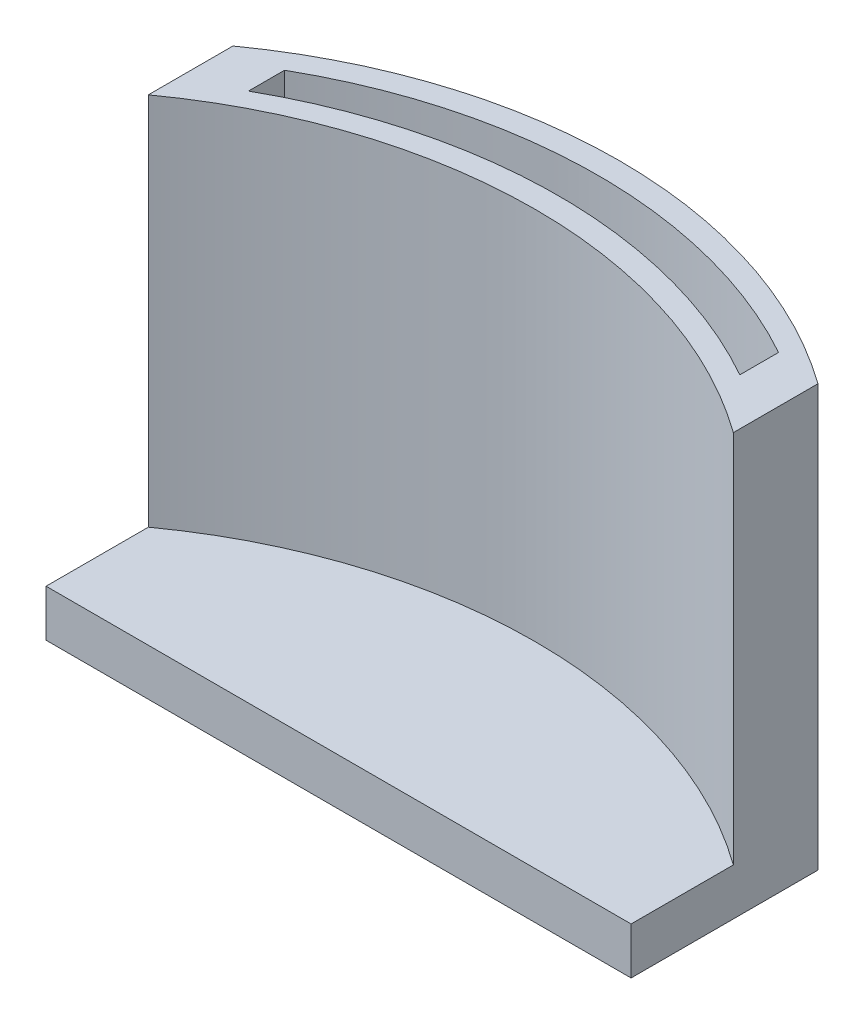
SolidWorks part; units mm, degrees
ref_plane "Front Plane" through (0, 0, 0) normal (0, 0, 1) x (1, 0, 0)
ref_plane "Top Plane" through (0, 0, 0) normal (0, 1, 0) x (1, 0, 0)
ref_plane "Right Plane" through (0, 0, 0) normal (1, 0, 0) x (0, 0, -1)
sketch "Sketch1" plane through (0, 0, 0) normal (0, 1, 0) x (1, 0, 0)
  line L1 (0, 0) -> (31.75, 0)
  line L2 (0, 0) -> (0, 26.6496)
  line L4 (31.75, 0) -> (31.75, 26.6496)
  arc A0 (0, 26.6496) -> (31.75, 26.6496) centre (15.875, 4.4945) cw
  dimension "D3" = 27.2555
  dimension "D4" = 4.4945
  dimension "D5" = 15.875
  dimension "D1" = 31.75
extrude "Boss-Extrude1" add sketch "Sketch1" along normal blind 2.54
sketch "Sketch2" plane through (0, 2.54, 0) normal (0, 1, 0) x (1, 0, 0)
  line L1 (0, 26.6496) -> (0, 0) construction
  line L3 (31.75, 0) -> (31.75, 26.6496) construction
  line L4 (31.75, 22.0596) -> (31.75, 26.6496)
  line L5 (0, 0) -> (31.75, 0) construction
  line L6 (0, 22.0596) -> (0, 26.6496)
  line L10 (2.54, 26.9117) -> (2.54, 24.9517)
  line L11 (29.21, 27.0547) -> (29.21, 24.9517)
  arc A1 (0, 22.0596) -> (31.75, 22.0596) centre (15.875, 0) cw
  arc A2 (2.54, 26.9117) -> (29.21, 27.0547) centre (16.002, 3.302) cw
  arc A3 (2.54, 24.9517) -> (29.21, 24.9517) centre (15.875, 1.27) cw
  arc A4 (0, 26.6496) -> (31.75, 26.6496) centre (15.875, 4.4945) cw
  point P20 (29.21, 26.0032)
  dimension "D2" = 27.178
  dimension "D3" = 0
  dimension "D4" = 15.875
  dimension "D7" = 27.178
  dimension "D8" = 27.178
  dimension "D9" = 3.302
  dimension "D10" = 16.002
  dimension "D11" = 1.27
  dimension "D12" = 15.875
  dimension "D13" = 4.4945
  dimension "D5" = 2.54
  dimension "D6" = 2.54
extrude "Boss-Extrude4" add sketch "Sketch2" along normal blind 20.32
sketch "Sketch3" plane through (0, 2.54, 0) normal (0, 1, 0) x (1, 0, 0)
  line L0 (31.75, 0) -> (31.75, 26.6496) construction
  line L1 (0, 0) -> (31.75, 0)
  line L2 (0, 0) -> (0, 16.51)
  line L3 (0, 16.51) -> (31.75, 16.51)
  line L4 (31.75, 0) -> (31.75, 16.51)
  dimension "D1" = 16.51
extrude "Cut-Extrude1" cut sketch "Sketch3" against normal blind 2.54
